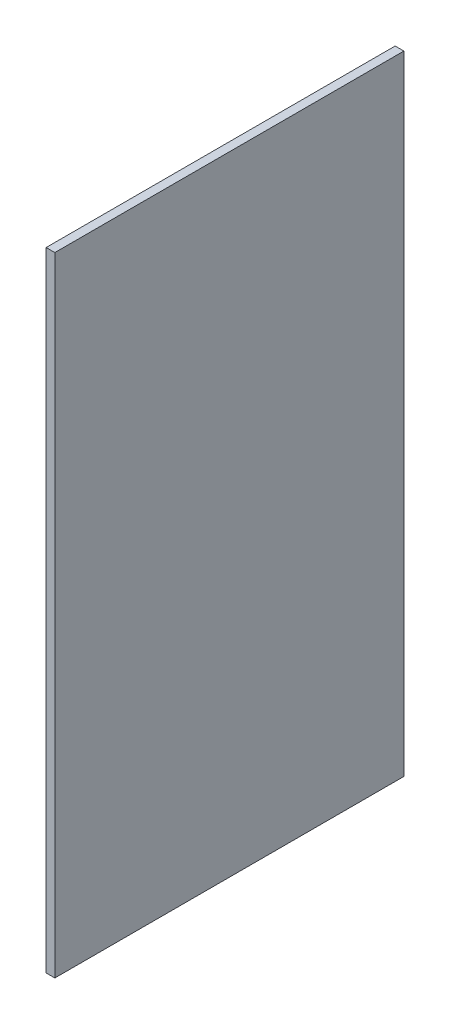
SolidWorks part; units mm, degrees
ref_plane "Front Plane" through (0, 0, 0) normal (0, 0, 1) x (1, 0, 0)
ref_plane "Top Plane" through (0, 0, 0) normal (0, 1, 0) x (1, 0, 0)
ref_plane "Right Plane" through (0, 0, 0) normal (1, 0, 0) x (0, 0, -1)
sketch "Sketch1" plane through (0, 0, 0) normal (1, 0, 0) x (0, -1, 0)
  line L1 (360, -200) -> (-360, -200)
  line L2 (360, -200) -> (360, 200)
  line L3 (360, 200) -> (-360, 200)
  line L4 (-360, -200) -> (-360, 200)
  line L5 (360, -200) -> (-360, 200) construction
  line L6 (360, 200) -> (-360, -200) construction
  point P0 (0, 0)
  dimension "D1" = 720
  dimension "D2" = 400
extrude "Boss-Extrude1" add sketch "Sketch1" along normal blind 10
